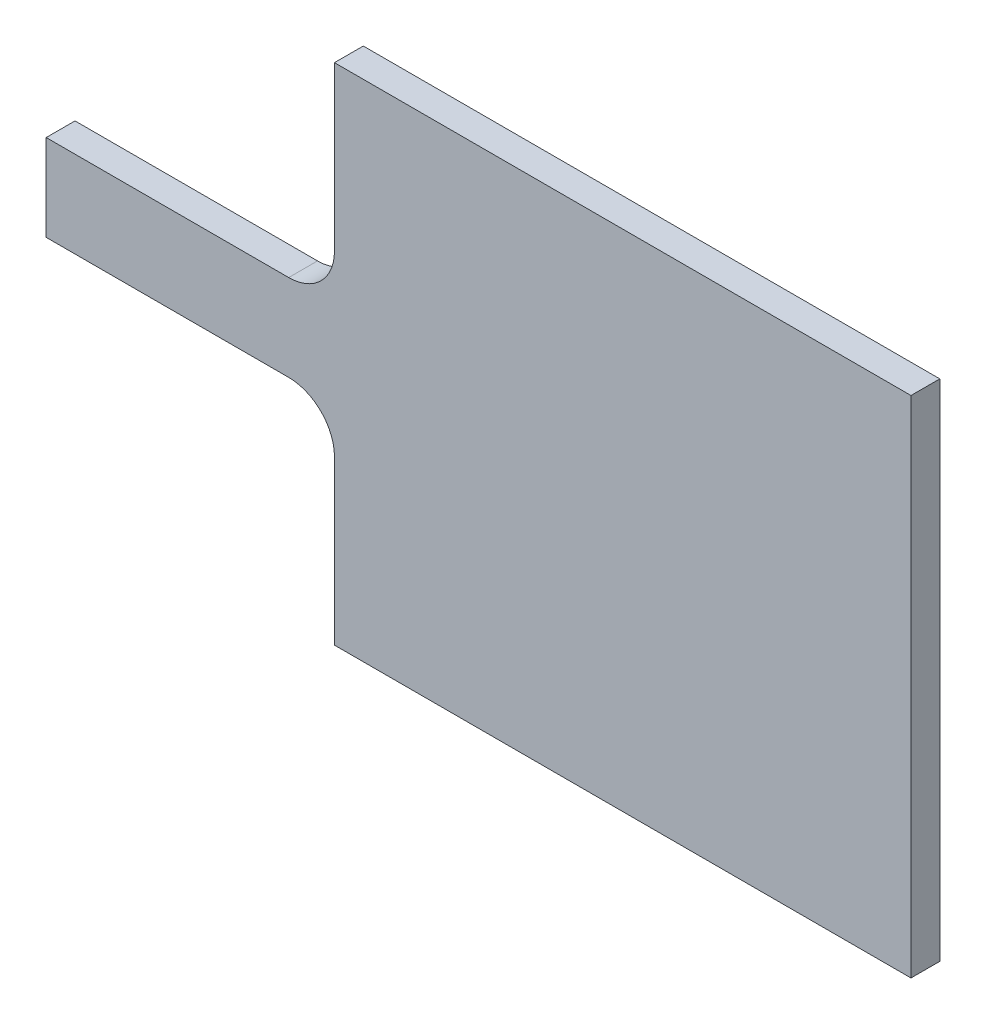
SolidWorks part; units mm, degrees
material "6061-T4 (SS)"
ref_plane "Front Plane" through (0, 0, 0) normal (0, 0, 1) x (1, 0, 0)
ref_plane "Top Plane" through (0, 0, 0) normal (0, 1, 0) x (1, 0, 0)
ref_plane "Right Plane" through (0, 0, 0) normal (1, 0, 0) x (0, 0, -1)
sketch "Sketch1" plane through (0, 0, 0) normal (0, 0, 1) x (1, 0, 0)
  line L0 (0, 11.8375) -> (0, 17.5)
  line L1 (0, 0) -> (20, 0)
  line L2 (0, 0) -> (0, 5.6625)
  line L3 (0, 17.5) -> (20, 17.5)
  line L4 (20, 0) -> (20, 17.5)
  line L5 (-1.5875, 10.25) -> (-10, 10.25)
  line L7 (-1.5875, 7.25) -> (-10, 7.25)
  line L8 (-10, 10.25) -> (-10, 7.25)
  line L9 (0, 7.25) -> (0, 10.25) construction
  arc A0 (0, 5.6625) -> (-1.5875, 7.25) centre (-1.5875, 5.6625) ccw
  arc A1 (-1.5875, 10.25) -> (0, 11.8375) centre (-1.5875, 11.8375) ccw
  dimension "D5" = 1.5875
  dimension "D1" = 17.5
  dimension "D2" = 20
  dimension "D3" = 3
  dimension "D4" = 10
extrude "Boss-Extrude1" add sketch "Sketch1" along normal blind 1
